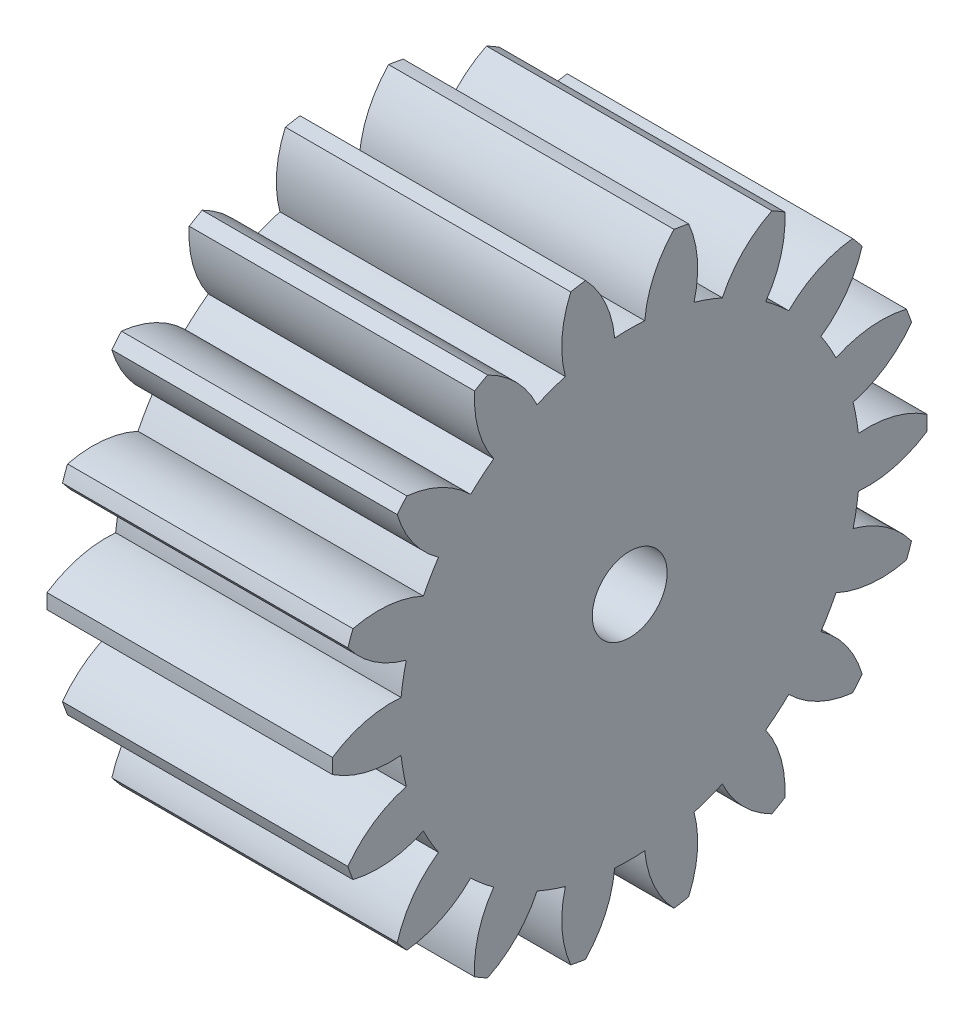
SolidWorks part; units mm, degrees
ref_plane "Plane1" through (0, 0, 0) normal (0, 0, 1) x (1, 0, 0)
ref_plane "Plane2" through (0, 0, 0) normal (0, 1, 0) x (1, 0, 0)
ref_plane "Plane3" through (0, 0, 0) normal (1, 0, 0) x (0, 0, -1)
other "Configuration Table"
sketch "HoldingSke" plane through (0, 0, 0) normal (0, 1, 0) x (1, 0, 0)
  line L0 (0, 0) -> (773.0187, -251.169)
  line L1 (-15, 0) -> (100, 0) construction
  line L2 (0, 0) -> (-2.1039, 2.3779)
  line L3 (0, 0) -> (-11.863, 4.5341)
  line L4 (0, 0) -> (8.2133, 2.6687)
  line L5 (0, 0) -> (-47.5972, -17.7524)
  line L6 (0, 0) -> (-6.3167, -4.2619)
  line L7 (-2.1039, 2.3779) -> (8.8308, 51.9871)
  line L8 (-76.2, 54.61) -> (-74.168, 54.61)
  line L9 (-71.009, 38.7566) -> (-53.1078, 45.2721)
  line L10 (-76.2, 71.12) -> (104.1128, 71.12)
  line L11 (0, 0) -> (-7.62, 0)
  line L12 (-76.2, 101.6) -> (-76.1716, 101.6)
  line L13 (24.9733, 27.94) -> (52.9518, 28.4284)
  line L14 (24.9733, 27.94) -> (25.0241, 27.9398)
  line L15 (24.9733, 27.94) -> (100.4021, 29.52)
  circle A0 centre (0, 0) radius 0.9995
  circle A1 centre (0, 0) radius 6.1404
  circle A2 centre (0, 0) radius 38.1
  circle A3 centre (0, 0) radius 0.9995
  dimension "MHD" = 12.2809
  dimension "Hub_dia" = 76.2
  dimension "Bore" = 1.999
  dimension "MBD" = 1.999
  dimension "Num_teeth" = 18
  dimension "Pitch" = 812.8
  dimension "Overall_len" = 50.8
  dimension "Show_teeth" = 18
  dimension "Thickness" = 7.62
  dimension "OAL" = 50.8001
  dimension "T_dim" = 2.032
  dimension "Ap" = 20
  dimension "H" = 19.05
  dimension "Pitch_radius" = 180.3128
  dimension "Width" = 7.62
  dimension "Backlash" = 0.0284
  dimension "Addendum_fac" = 1
  dimension "Dedendum_fac" = 1.2
  dimension "Clearance_fac" = 0.2
  dimension "Dedendum_add" = 0.0508
sketch "BasProSke" plane through (0, 0, 0) normal (0, 1, 0) x (1, 0, 0)
  line L0 (-10, 0) -> (60, 0) construction
  line L1 (0, 0) -> (0, 7.9375)
  line L2 (0, 0) -> (7.62, 0)
  line L3 (7.62, 0) -> (7.62, 7.9375)
  line L4 (7.62, 7.9375) -> (0, 7.9375)
  dimension "Thickness" = 7.62
  dimension "Diameter" = 15.875
revolve "Base-Revolve" add sketch "BasProSke" angle 360 about L0
sketch "TooCutSke" plane through (0, 0, 0) normal (1, 0, 0) x (0, 0, -1)
  line L1 (0, 0) -> (0, 107) construction
  line L2 (0, 0) -> (-0.6724, 7.112) construction
  line L3 (0, 0) -> (-2.473, 14.0251) construction
  line L4 (-0.6724, 7.112) -> (-1.2365, 7.0126) construction
  arc A0 (0.4018, 6.1273) -> (-0.4018, 6.1273) centre (0, 0) ccw
  arc A1 (1.2039, 7.8714) -> (-1.2039, 7.8714) centre (0, 0) ccw
  circle A2 centre (0, 0) radius 7.1438 construction
  circle A3 centre (0, 0) radius 6.7129 construction
  arc A4 (-0.4018, 6.1273) -> (-1.2039, 7.8714) centre (-3.2481, 5.8748) ccw
  arc A5 (1.2039, 7.8714) -> (0.4018, 6.1273) centre (3.2481, 5.8748) ccw
  dimension "Root_dia" = 12.2809
  dimension "Overcut_dia" = 15.9258
  dimension "Pitch_dia" = 14.2875
  dimension "Base_dia" = 13.4259
  dimension "Flank_rad" = 2.8575
  dimension "Half_ang" = 10
  dimension "Half_CT" = 0.5728
extrude "ToothCut" cut sketch "TooCutSke" along normal through all
fillet "Breaks" [suppressed] radius 0.0159
fillet "RootFillets" [suppressed] radius 0.2095
pattern_circular "TeethCuts" count 18 every 20 about axis through (-10, 0, 0) along (1, 0, 0) of "ToothCut", "RootFillets", "Breaks"
sketch "HubNeaOneSke" plane through (0, 0, 0) normal (-1, 0, 0) x (0, 0, 1)
  circle A0 centre (0, 0) radius 6.1404
  dimension "Diameter" = 12.2809
extrude "HubNearOne" [suppressed] add sketch "HubNeaOneSke" along normal blind 43.1801
sketch "HubNeaBotSke" plane through (0, 0, 0) normal (-1, 0, 0) x (0, 0, 1)
  circle A0 centre (0, 0) radius 6.1404
  dimension "Diameter" = 12.2809
extrude "HubNearBoth" [suppressed] add sketch "HubNeaBotSke" along normal blind 21.59
ref_plane "FarPln" through (7.62, 0, 0) normal (1, 0, 0) x (0, 0, -1)
sketch "HubFarSke" plane through (7.62, 0, 0) normal (1, 0, 0) x (0, 0, -1)
  circle A0 centre (0, 0) radius 6.1404
  dimension "Diameter" = 12.2809
extrude "HubFar" [suppressed] add sketch "HubFarSke" along normal blind 21.59
sketch "BorSke" plane through (0, 0, 0) normal (1, 0, 0) x (0, 0, -1)
  circle A0 centre (0, 0) radius 0.9995
  dimension "Diameter" = 1.999
extrude "Bore" cut sketch "BorSke" along normal mid plane 101.6001
sketch "KeySke" plane through (0, 0, 0) normal (1, 0, 0) x (0, 0, -1)
  line L0 (-0.127, 0) -> (-0.127, 1.0325)
  line L1 (-0.127, 1.0325) -> (0.127, 1.0325)
  line L2 (0.127, 1.0325) -> (0.127, 0)
  line L3 (0, 0) -> (0, 34) construction
  line L4 (-0.127, 0) -> (0.127, 0)
  dimension "Offset" = 1.0325
  dimension "Width" = 0.254
extrude "Keyway" [suppressed] cut sketch "KeySke" along normal mid plane 101.6001
pattern_circular "Keyway2" [suppressed] count 2 every 90 about axis through (-10, 0, 0) along (1, 0, 0)
sketch3d "3DSketch1"
  point P0 (3.81, 0, 7.9375)
equation "' \"Pitch@HoldingSke\" = 4"
equation "' \"Num_teeth@HoldingSke\" = 12"
equation "' \"Ap@HoldingSke\" =  20"
equation "' \"Ap@HoldingSke\" = 20"
equation "' \"Width@HoldingSke\" = 0.5"
equation "' \"Hub_dia@HoldingSke\"= 1"
equation "' \"Hub_dia@HoldingSke\" = 1"
equation "' \"Overall_len@HoldingSke\" = 1.0"
equation "' \"Bore@HoldingSke\" = 0.75"
equation "' \"T_dim@HoldingSke\" = 0.85"
equation "' \"Width@KeySke\" = 0.25"
equation "' \"Show_teeth@HoldingSke\" = 13"
equation "' \"Backlash@HoldingSke\" = 0.009"
equation "' \"Addendum_fac@HoldingSke\" = 1.0"
equation "' \"Dedendum_fac@HoldingSke\" = 1.25"
equation "' \"Dedendum_add@HoldingSke\" = 0.00005"
equation "' \"Clearance_fac@HoldingSke\" = 0.25"
equation "' \"Pitch@HoldingSke\" = 0.5"
equation "' \"Num_teeth@HoldingSke\" = 23"
equation "' \"Show_teeth@HoldingSke\" = 23"
equation "' \"Backlash@HoldingSke\" = 0.0375"
equation "\"Overcut_dia@TooCutSke\" = (\"Num_teeth@HoldingSke\" + 2 * \"Addendum_fac@HoldingSke\") / \"Pitch@HoldingSke\" + 0.002"
equation "\"Pitch_dia@TooCutSke\" = \"Num_teeth@HoldingSke\" / \"Pitch@HoldingSke\""
equation "\"Base_dia@TooCutSke\" = \"Num_teeth@HoldingSke\" / \"Pitch@HoldingSke\" * cos((\"Ap@HoldingSke\"  * 3.14159265 / 180))"
equation "\"Root_dia@TooCutSke\" = (\"Num_teeth@HoldingSke\" + 2) / \"Pitch@HoldingSke\" - 2 * (\"Addendum_fac@HoldingSke\" + \"Dedendum_fac@HoldingSke\") / \"Pitch@HoldingSke\" - \"Dedendum_add@HoldingSke\" * 2"
equation "\"Half_ang@TooCutSke\" = 180 / \"Num_teeth@HoldingSke\""
equation "\"Half_CT@TooCutSke\" = \"Num_teeth@HoldingSke\" / \"Pitch@HoldingSke\" * sin((3.14159265 / 2 / \"Num_teeth@HoldingSke\")) / 2 - 7 * \"Backlash@HoldingSke\" / 4"
equation "\"Flank_rad@TooCutSke\" = \"Num_teeth@HoldingSke\" / \"Pitch@HoldingSke\" / 5"
equation "\"Radius@RootFillets\" = \"Clearance_fac@HoldingSke\" / \"Pitch@HoldingSke\" + \"Dedendum_add@HoldingSke\""
equation "\"Break_rad@Breaks\" = 0.02 / \"Pitch@HoldingSke\""
equation "\"Thickness@HoldingSke\" = \"Width@HoldingSke\""
equation "\"OAL@HoldingSke\" = \"Thickness@HoldingSke\""
equation "\"MHD@HoldingSke\" = (\"Num_teeth@HoldingSke\" + 2) / \"Pitch@HoldingSke\" - 2 * (\"Addendum_fac@HoldingSke\" + \"Dedendum_fac@HoldingSke\")  / \"Pitch@HoldingSke\" - \"Dedendum_add@HoldingSke\" * 2"
equation "\"MBD@HoldingSke\" = (\"Num_teeth@HoldingSke\" + 2) / \"Pitch@HoldingSke\" - 2 * (\"Addendum_fac@HoldingSke\" + \"Dedendum_fac@HoldingSke\")  / \"Pitch@HoldingSke\" - \"Dedendum_add@HoldingSke\" * 2 - 0.002"
equation "\"MHD@HoldingSke\" = ((sgn( \"MHD@HoldingSke\" - \"Hub_dia@HoldingSke\" )-1)*( \"MHD@HoldingSke\" - \"Hub_dia@HoldingSke\" ))/-2+ \"Hub_dia@HoldingSke\""
equation "\"MBD@HoldingSke\" = ((sgn( \"MBD@HoldingSke\" - \"Bore@HoldingSke\" )-1)*( \"MBD@HoldingSke\" - \"Bore@HoldingSke\" ))/-2+ \"Bore@HoldingSke\""
equation "\"OAL@HoldingSke\" = ((sgn( \"OAL@HoldingSke\" - \"Overall_len@HoldingSke\" )+1)*( \"OAL@HoldingSke\" - \"Overall_len@HoldingSke\" ))/2 + \"Overall_len@HoldingSke\" + 0.000002"
equation "\"Num_teeth@TeethCuts\" = int( \"Show_teeth@HoldingSke\" ) + 1"
equation "\"Num_teeth@TeethCuts\" = ((sgn( \"Num_teeth@TeethCuts\" - \"Num_teeth@HoldingSke\" )-1)*( \"Num_teeth@TeethCuts\" - \"Num_teeth@HoldingSke\" ))/-2+ \"Num_teeth@HoldingSke\""
equation "\"Num_teeth@TeethCuts\" = ((sgn( \"Num_teeth@TeethCuts\" - 2.0)+1)*( \"Num_teeth@TeethCuts\" - 2.0))/2 +2.0"
equation "\"Angle@TeethCuts\" = 360.0 / \"Num_teeth@HoldingSke\""
equation "\"Diameter@BasProSke\" = (\"Num_teeth@HoldingSke\" + 2 * \"Addendum_fac@HoldingSke\") / \"Pitch@HoldingSke\""
equation "\"Thickness@BasProSke\"  = \"Thickness@HoldingSke\""
equation "' \"Fillet_rad@BasProSke\" =  \"Thickness@HoldingSke\" * 0.05"
equation "' \"Fillet_rad@BasProSke\" = \"Thickness@HoldingSke\" * 0.05"
equation "\"MHD@HoldingSke\" = ((sgn( \"MHD@HoldingSke\" - \"Root_dia@TooCutSke\" )-1)*( \"MHD@HoldingSke\" - \"Root_dia@TooCutSke\" ))/-2+ \"Root_dia@TooCutSke\""
equation "\"Diameter@HubNeaOneSke\" = \"MHD@HoldingSke\""
equation "\"Length@HubNearOne\" = \"OAL@HoldingSke\" - \"Thickness@BasProSke\""
equation "\"Diameter@HubNeaBotSke\" = \"MHD@HoldingSke\""
equation "\"Length@HubNearBoth\" = ( \"OAL@HoldingSke\" - \"Thickness@BasProSke\" ) / 2.0"
equation "\"Thickness@FarPln\" = \"Thickness@BasProSke\""
equation "\"Diameter@HubFarSke\" = \"MHD@HoldingSke\""
equation "\"Length@HubFar\" = ( \"OAL@HoldingSke\" - \"Thickness@BasProSke\" ) / 2.0"
equation "\"Diameter@BorSke\" = \"MBD@HoldingSke\""
equation "\"D1@Bore\" = \"OAL@HoldingSke\" * 2.0"
equation "\"D1@Keyway\" = \"OAL@HoldingSke\" * 2.0"
equation "\"Offset@KeySke\" = \"T_dim@HoldingSke\" - \"MBD@HoldingSke\" / 2.0"
